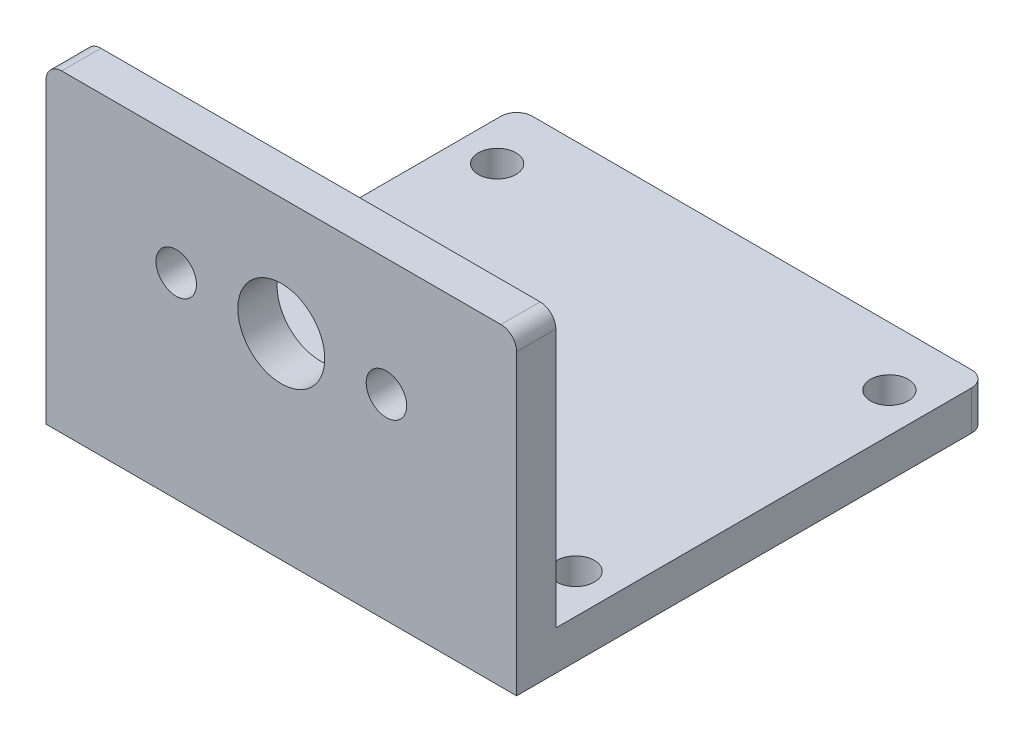
SolidWorks part; units mm, degrees
ref_plane "Front Plane" through (0, 0, 0) normal (0, 0, 1) x (1, 0, 0)
ref_plane "Top Plane" through (0, 0, 0) normal (0, 1, 0) x (1, 0, 0)
ref_plane "Right Plane" through (0, 0, 0) normal (1, 0, 0) x (0, 0, -1)
sketch "Sketch2" plane through (0, 0, 0) normal (1, 0, 0) x (0, 0, -1)
  line L0 (0, 0) -> (38.1, 0)
  line L1 (38.1, 0) -> (38.1, 3.175)
  line L2 (38.1, 3.175) -> (3.175, 3.175)
  line L3 (3.175, 3.175) -> (3.175, 25.4)
  line L4 (3.175, 25.4) -> (0, 25.4)
  line L5 (0, 25.4) -> (0, 0)
  dimension "D1" = 3.175
  dimension "D2" = 3.175
  dimension "D3" = 25.4
  dimension "D4" = 38.1
extrude "Boss-Extrude1" add sketch "Sketch2" along normal blind 38.1
sketch "Sketch3" plane through (0, 0, -3.175) normal (0, 0, -1) x (-1, 0, 0)
  line L0 (-38.1, 3.175) -> (0, 3.175) construction
  line L1 (0, 3.175) -> (0, 25.4) construction
  circle A0 centre (-19.05, 15.875) radius 3.5179
  circle A1 centre (-10.541, 15.875) radius 1.6383
  circle A2 centre (-27.559, 15.875) radius 1.6383
  dimension "D1" = 8.509
  dimension "D2" = 8.509
  dimension "D3" = 3.2766
  dimension "D4" = 3.2766
  dimension "D6" = 7.0358
  dimension "D5" = 12.7
  dimension "D7" = 19.05
extrude "Cut-Extrude1" cut sketch "Sketch3" against normal through all
fillet "Fillet1" radius 1.27 4 edges at (0, 25.4, -1.5875) (38.1, 25.4, -1.5875) (0, 1.5875, -38.1) (38.1, 1.5875, -38.1)
sketch "Sketch4" plane through (0, 3.175, 0) normal (0, 1, 0) x (1, 0, 0)
  line L0 (0, 36.83) -> (0, 3.175) construction
  line L1 (38.1, 36.83) -> (38.1, 3.175) construction
  line L2 (36.83, 38.1) -> (1.27, 38.1) construction
  circle A0 centre (3.175, 7.9502) radius 1.524
  circle A1 centre (3.175, 33.3502) radius 1.524
  circle A2 centre (34.925, 33.3502) radius 1.524
  circle A3 centre (34.925, 7.9502) radius 1.524
  dimension "D1" = 3.175
  dimension "D3" = 3.175
  dimension "D4" = 3.175
  dimension "D7" = 25.4
  dimension "D8" = 25.4
  dimension "D2" = 3.175
  dimension "D5" = 4.7498
  dimension "D6" = 4.7498
extrude "Cut-Extrude2" cut sketch "Sketch4" against normal through all
